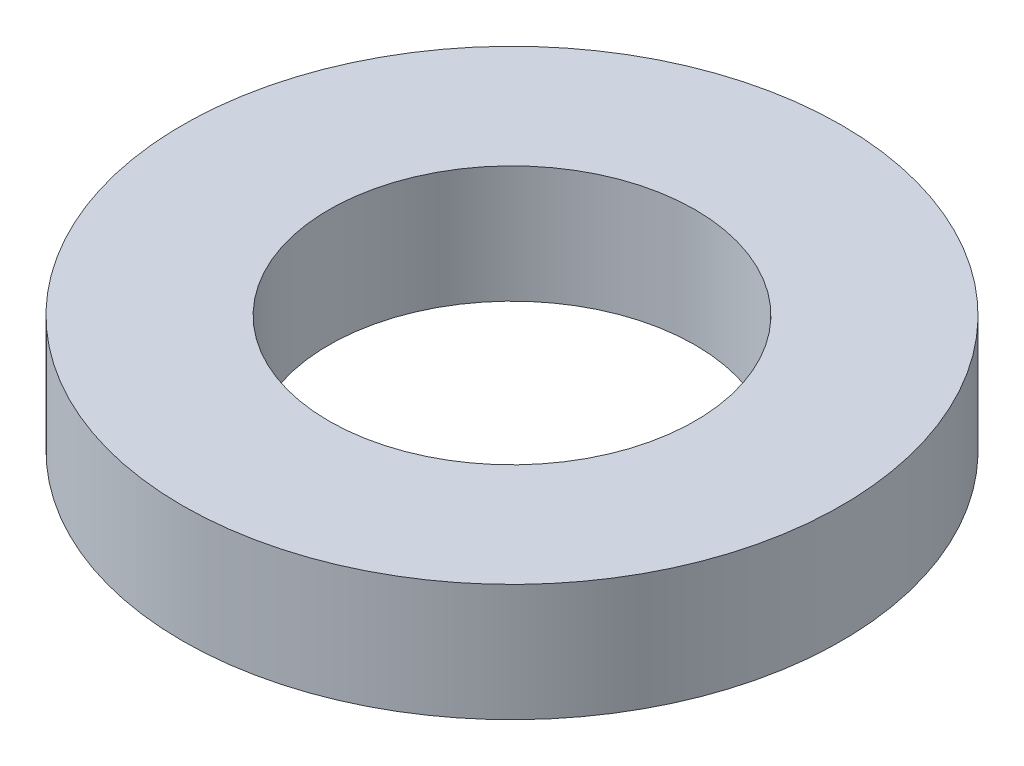
SolidWorks part; units mm, degrees
material "硅橡胶"
ref_plane "前视基准面" through (0, 0, 0) normal (0, 0, 1) x (1, 0, 0)
ref_plane "上视基准面" through (0, 0, 0) normal (0, 1, 0) x (1, 0, 0)
ref_plane "右视基准面" through (0, 0, 0) normal (1, 0, 0) x (0, 0, -1)
sketch "草图1" plane through (0, 0, 0) normal (0, 1, 0) x (1, 0, 0)
  circle A0 centre (0, 0) radius 12.5
  circle A1 centre (0, 0) radius 22.5
  dimension "D1" = 25
  dimension "D2" = 45
extrude "凸台-拉伸1" add sketch "草图1" along normal mid plane 8
